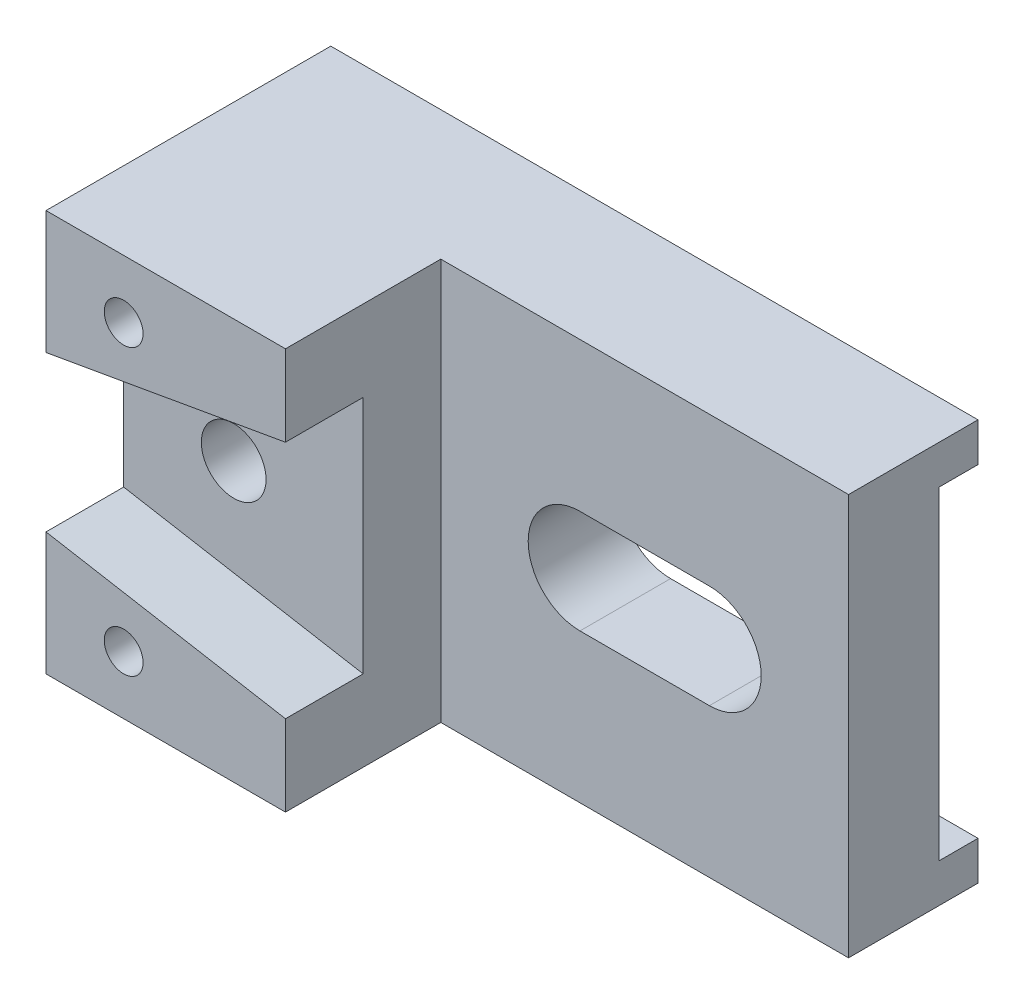
SolidWorks part; units mm, degrees
ref_plane "Front Plane" through (0, 0, 0) normal (0, 0, 1) x (1, 0, 0)
ref_plane "Top Plane" through (0, 0, 0) normal (0, 1, 0) x (1, 0, 0)
ref_plane "Right Plane" through (0, 0, 0) normal (1, 0, 0) x (0, 0, -1)
sketch "Sketch1" plane through (0, 0, 0) normal (0, 0, 1) x (1, 0, 0)
  line L1 (-50, 31) -> (50, 31)
  line L2 (-50, 31) -> (-50, -31)
  line L3 (-50, -31) -> (50, -31)
  line L4 (50, 31) -> (50, -31)
  line L5 (-50, 31) -> (50, -31) construction
  line L6 (-50, -31) -> (50, 31) construction
  point P0 (0, 0)
  dimension "D1" = 62
  dimension "D2" = 100
extrude "Boss-Extrude1" add sketch "Sketch1" along normal blind 20
sketch "Sketch2" plane through (0, 0, 20) normal (0, 0, 1) x (1, 0, 0)
  line L0 (-13, 31) -> (-13, -31)
  line L1 (50, 31) -> (-50, 31) construction
  line L2 (-50, -31) -> (50, -31) construction
  line L3 (-50, 31) -> (-50, -31) construction
  line L8 (50, -31) -> (50, 31)
  line L9 (50, 31) -> (-50, 31)
  line L10 (-50, 31) -> (-50, -31)
  line L11 (-50, -31) -> (50, -31)
  line L13 (-13, 31) -> (-50, 31)
  line L14 (-50, 31) -> (-50, -31)
  line L15 (-50, -31) -> (-13, -31)
  dimension "D1" = 37
  dimension "D2" = 0
extrude "Boss-Extrude2" add sketch "Sketch2" along normal blind 24
sketch "Sketch3" plane through (0, 0, 44) normal (0, 0, 1) x (1, 0, 0)
  line L0 (0, 0) -> (-69.7551, 0) construction
  line L1 (-50, 12) -> (-13, 18.5)
  line L2 (-50, 31) -> (-50, -31) construction
  line L3 (-13, -31) -> (-13, 31) construction
  line L4 (-13, 18.5) -> (-13, -18.5)
  line L5 (-13, -18.5) -> (-50, -12)
  line L6 (-50, -12) -> (-50, 12)
  dimension "D1" = 37
  dimension "D2" = 24
extrude "Cut-Extrude2" cut sketch "Sketch3" against normal blind 12 contours L6 L1 L4 L5
sketch "Sketch4" plane through (0, 0, 32) normal (0, 0, 1) x (1, 0, 0)
  line L0 (-13, 18.5) -> (-13, -18.5) construction
  circle A0 centre (-33, 0) radius 5
  dimension "D1" = 10
  dimension "D2" = 20
extrude "Cut-Extrude3" cut sketch "Sketch4" against normal through all
sketch "Sketch5" plane through (0, 0, 44) normal (0, 0, 1) x (1, 0, 0)
  line L0 (-13, 31) -> (-50, 31) construction
  line L3 (-50, 31) -> (-50, 12) construction
  circle A0 centre (-38, 22) radius 3
  point P6 (-50, 19.1397)
  point P7 (-50, 23.8939)
  dimension "D1" = 6
  dimension "D2" = 9
  dimension "D3" = 12
extrude "Cut-Extrude4" cut sketch "Sketch5" against normal blind 20
sketch "Sketch12" plane through (0, 0, 44) normal (0, 0, 1) x (1, 0, 0)
  line L0 (-50, -31) -> (-13, -31) construction
  line L1 (-50, -12) -> (-50, -31) construction
  circle A0 centre (-38, -22) radius 3
  dimension "D1" = 6
  dimension "D2" = 9
  dimension "D3" = 12
extrude "Cut-Extrude12" cut sketch "Sketch12" against normal blind 20
sketch "Sketch13" plane through (0, 0, 20) normal (0, 0, 1) x (1, 0, 0)
  line L0 (8.5, 0) -> (28.5, 0) construction
  line L1 (8.5, 8) -> (28.5, 8)
  line L2 (8.5, -8) -> (28.5, -8)
  line L3 (50, -31) -> (50, 31) construction
  arc A0 (8.5, 8) -> (8.5, -8) centre (8.5, 0) ccw
  arc A1 (28.5, -8) -> (28.5, 8) centre (28.5, 0) ccw
  point P3 (18.5, 0)
  point P12 (26.0468, 31)
  dimension "D2" = 8
  dimension "D3" = 21.5
  dimension "D1" = 20
extrude "Cut-Extrude13" cut sketch "Sketch13" against normal through all contours L2 A1 L1 A0
sketch "Sketch14" plane through (50, 0, 0) normal (1, 0, 0) x (0, 0, -1)
  line L0 (0, -31) -> (0, 31) construction
  line L1 (0, -25) -> (-6, -25)
  line L2 (-6, -25) -> (-6, 25)
  line L3 (-6, 25) -> (0, 25)
  line L4 (0, 25) -> (0, -25)
  dimension "D1" = 6
  dimension "D2" = 6
  dimension "D3" = 6
extrude "Cut-Extrude14" cut sketch "Sketch14" against normal through all
